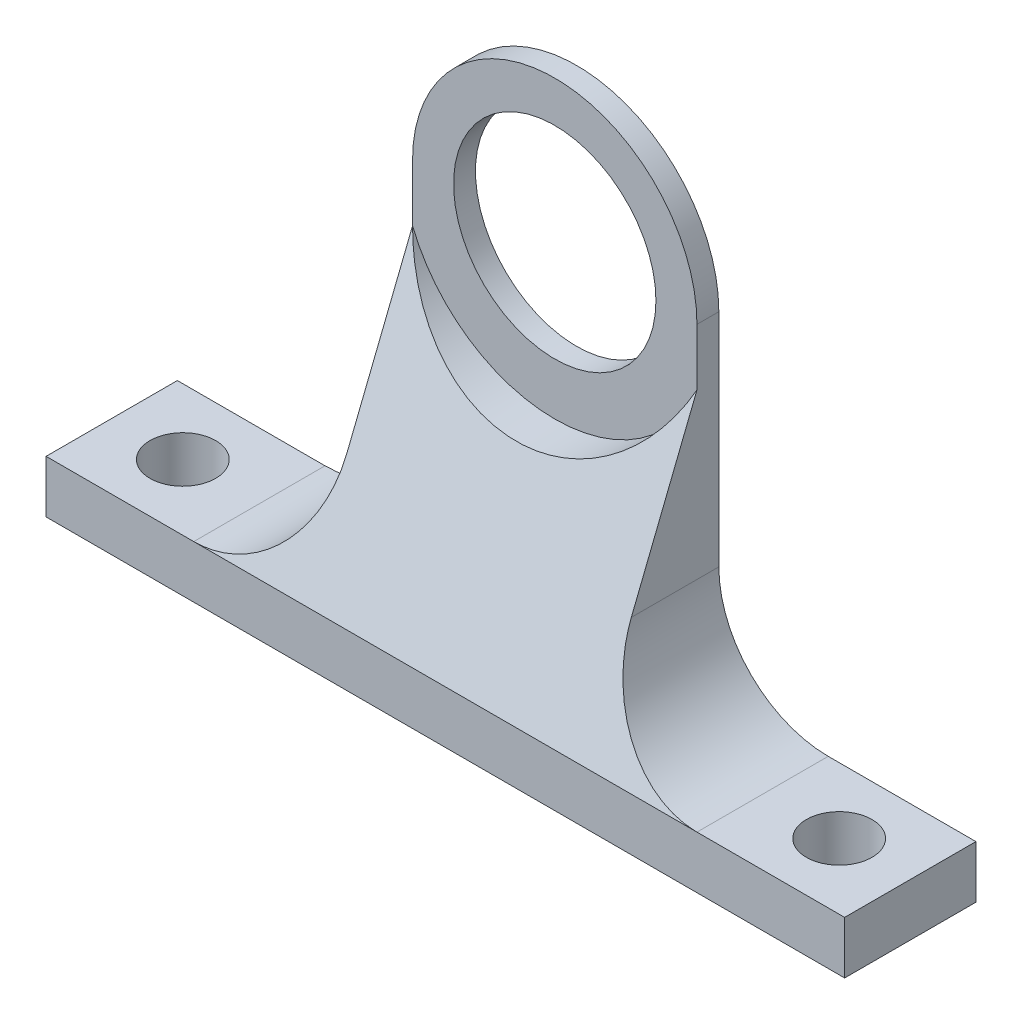
SolidWorks part; units mm, degrees
ref_plane "Front Plane" through (0, 0, 0) normal (0, 0, 1) x (1, 0, 0)
ref_plane "Top Plane" through (0, 0, 0) normal (0, 1, 0) x (1, 0, 0)
ref_plane "Right Plane" through (0, 0, 0) normal (1, 0, 0) x (0, 0, -1)
sketch "Sketch1" plane through (0, 0, 0) normal (0, 0, 1) x (1, 0, 0)
  line L0 (-36.5, 0) -> (36.5, 0)
  line L1 (36.5, 0) -> (36.5, 4.8)
  line L2 (36.5, 4.8) -> (23, 4.8)
  line L3 (13, 14.8) -> (13, 35)
  line L4 (-36.5, 0) -> (-36.5, 4.8)
  line L5 (-36.5, 4.8) -> (-23, 4.8)
  line L6 (-13, 14.8) -> (-13, 35)
  circle A0 centre (0, 35) radius 9.25
  arc A1 (13, 35) -> (-13, 35) centre (0, 35) ccw
  arc A2 (23, 4.8) -> (13, 14.8) centre (23, 14.8) cw
  arc A3 (-23, 4.8) -> (-13, 14.8) centre (-23, 14.8) ccw
  dimension "D2" = 18.5
  dimension "D4" = 26
  dimension "D5" = 10
  dimension "D7" = 10
  dimension "D1" = 35
  dimension "D3" = 73
  dimension "D6" = 4.8
extrude "Boss-Extrude1" add sketch "Sketch1" along normal blind 12
sketch "Sketch2" plane through (0, 4.8, 0) normal (0, 1, 0) x (1, 0, 0)
  line L0 (30, -6) -> (-30, -6) construction
  line L1 (0, 0) -> (0, -6) construction
  line L2 (-30, -6) -> (-36.5, -6) construction
  line L3 (-36.5, -12) -> (-36.5, 0) construction
  circle A0 centre (-30, -6) radius 3
  circle A1 centre (30, -6) radius 3
  dimension "D1" = 60
  dimension "D2" = 6
  dimension "D3" = 6
extrude "Cut-Extrude1" cut sketch "Sketch2" against normal through all
sketch "Sketch3" plane through (0, 0, 12) normal (0, 0, 1) x (1, 0, 0)
  circle A0 centre (0, 35) radius 14
  circle A1 centre (0, 35) radius 9.25 construction
  dimension "D1" = 28
extrude "Cut-Extrude2" cut sketch "Sketch3" against normal offset from surface (10 mm away) 2 up to face at (0, 12.7658, 0)
sketch "Sketch4" plane through (-36.5, 0, 0) normal (-1, 0, 0) x (0, 0, 1)
  line L0 (2, 29.8038) -> (12, 4.8)
  line L1 (12, 4.8) -> (12, 29.8038)
  line L2 (12, 29.8038) -> (2, 29.8038)
extrude "Cut-Extrude3" cut sketch "Sketch4" against normal through all
